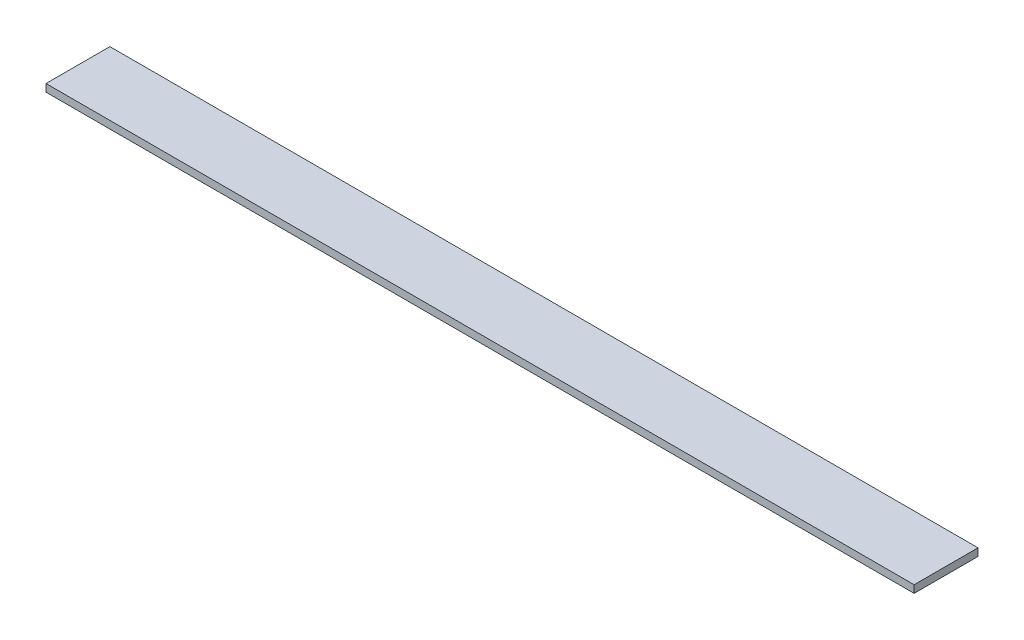
SolidWorks part; units mm, degrees
ref_plane "Front Plane" through (0, 0, 0) normal (0, 0, 1) x (1, 0, 0)
ref_plane "Top Plane" through (0, 0, 0) normal (0, 1, 0) x (1, 0, 0)
ref_plane "Right Plane" through (0, 0, 0) normal (1, 0, 0) x (0, 0, -1)
sketch "Sketch1" plane through (0, 0, 0) normal (0, 1, 0) x (1, 0, 0)
  line L1 (0, 0) -> (115.5, 0)
  line L2 (0, 0) -> (0, -8.5)
  line L3 (0, -8.5) -> (115.5, -8.5)
  line L4 (115.5, 0) -> (115.5, -8.5)
  dimension "D1" = 115.5
  dimension "D2" = 8.5
extrude "Boss-Extrude1" add sketch "Sketch1" against normal blind 1
sketch "Sketch2" [suppressed] plane through (0, 0, 0) normal (0, 1, 0) x (1, 0, 0)
  line L0 (229, -12.7) -> (229, 0) construction
  line L1 (0, -12.7) -> (229, -12.7)
  line L2 (0, -12.7) -> (0, -6)
  line L3 (0, -6) -> (229, -6)
  line L4 (229, -12.7) -> (229, -6)
  line L5 (229, 0) -> (0, 0) construction
  dimension "D1" = 6
extrude "Cut-Extrude1" [suppressed] cut sketch "Sketch2" against normal through all
sketch "Sketch3" [suppressed] plane through (0, 0, 0) normal (0, 1, 0) x (1, 0, 0)
  line L0 (102.5, -8.5) -> (102.5, 0) construction
  line L1 (0, -12.7) -> (229, -12.7)
  line L2 (0, -12.7) -> (0, -8.5)
  line L3 (0, -8.5) -> (229, -8.5)
  line L4 (229, -12.7) -> (229, -8.5)
  line L5 (102.5, 0) -> (0, 0) construction
  dimension "D1" = 8.5
extrude "Cut-Extrude2" [suppressed] cut sketch "Sketch3" against normal through all
sketch "Sketch4" [suppressed] plane through (0, 0, 0) normal (0, 1, 0) x (1, 0, 0)
  line L0 (102.5, 0) -> (0, 0) construction
  line L1 (102.5, -8.5) -> (6, -8.5)
  line L2 (102.5, -8.5) -> (102.5, 0)
  line L3 (102.5, 0) -> (6, 0)
  line L4 (6, -8.5) -> (6, 0)
  line L5 (0, 0) -> (0, -8.5) construction
  line L7 (6, -8.5) -> (0, -8.5)
  line L8 (6, -8.5) -> (6, -7.5)
  line L9 (6, -7.5) -> (0, -7.5)
  line L10 (0, -8.5) -> (0, -7.5)
  line M4 (0, -8.5) -> (102.5, -8.5)
  line M5 (102.5, -8.5) -> (102.5, 0)
  line M6 (102.5, 0) -> (0, 0)
  dimension "D1" = 6
  dimension "D2" = 7.5
extrude "Cut-Extrude3" [suppressed] cut sketch "Sketch4" against normal through all contours L4 M4 M5 M6 | L7 L10 L9 L8
sketch "Sketch5" [suppressed] plane through (0, 0, 0) normal (0, 1, 0) x (1, 0, 0)
  line L0 (228.6, 0) -> (0, 0) construction
  line L1 (228.6, -12.7) -> (9.3, -12.7)
  line L2 (228.6, -12.7) -> (228.6, 0)
  line L3 (228.6, 0) -> (9.3, 0)
  line L4 (9.3, -12.7) -> (9.3, 0)
  line L6 (0, -12.7) -> (9.3, -12.7)
  line L7 (0, -12.7) -> (0, -9.3)
  line L8 (0, -9.3) -> (9.3, -9.3)
  line L9 (9.3, -12.7) -> (9.3, -9.3)
  dimension "D1" = 9.3
  dimension "D2" = 9.3
extrude "Cut-Extrude4" [suppressed] cut sketch "Sketch5" against normal through all
sketch "Sketch6" [suppressed] plane through (0, -0.8, 0) normal (0, -1, 0) x (1, 0, 0)
  line L0 (0, 12.7) -> (228.6, 12.7) construction
  line L1 (228.6, 0) -> (9.3, 0)
  line L2 (228.6, 0) -> (228.6, 12.7)
  line L3 (228.6, 12.7) -> (9.3, 12.7)
  line L4 (9.3, 0) -> (9.3, 12.7)
  line L5 (228.6, 0) -> (0, 0) construction
  line L6 (0, 12.7) -> (9.3, 12.7)
  line L7 (0, 12.7) -> (0, 6.2)
  line L8 (0, 6.2) -> (9.3, 6.2)
  line L9 (9.3, 12.7) -> (9.3, 6.2)
  dimension "D1" = 9.3
  dimension "D2" = 6.2
extrude "Cut-Extrude5" [suppressed] cut sketch "Sketch6" against normal through all
sketch "Sketch7" [suppressed] plane through (0, -0.8, 0) normal (0, -1, 0) x (1, 0, 0)
  line L0 (0, 12.7) -> (228.6, 12.7) construction
  line L1 (228.6, 0) -> (8.5, 0)
  line L2 (228.6, 0) -> (228.6, 12.7)
  line L3 (228.6, 12.7) -> (8.5, 12.7)
  line L4 (8.5, 0) -> (8.5, 12.7)
  line L6 (0, 12.7) -> (8.5, 12.7)
  line L7 (0, 12.7) -> (0, 6.2)
  line L8 (0, 6.2) -> (8.5, 6.2)
  line L9 (8.5, 12.7) -> (8.5, 6.2)
  line L10 (228.6, 0) -> (0, 0) construction
  dimension "D1" = 8.5
  dimension "D2" = 6.2
extrude "Cut-Extrude6" [suppressed] cut sketch "Sketch7" against normal through all
